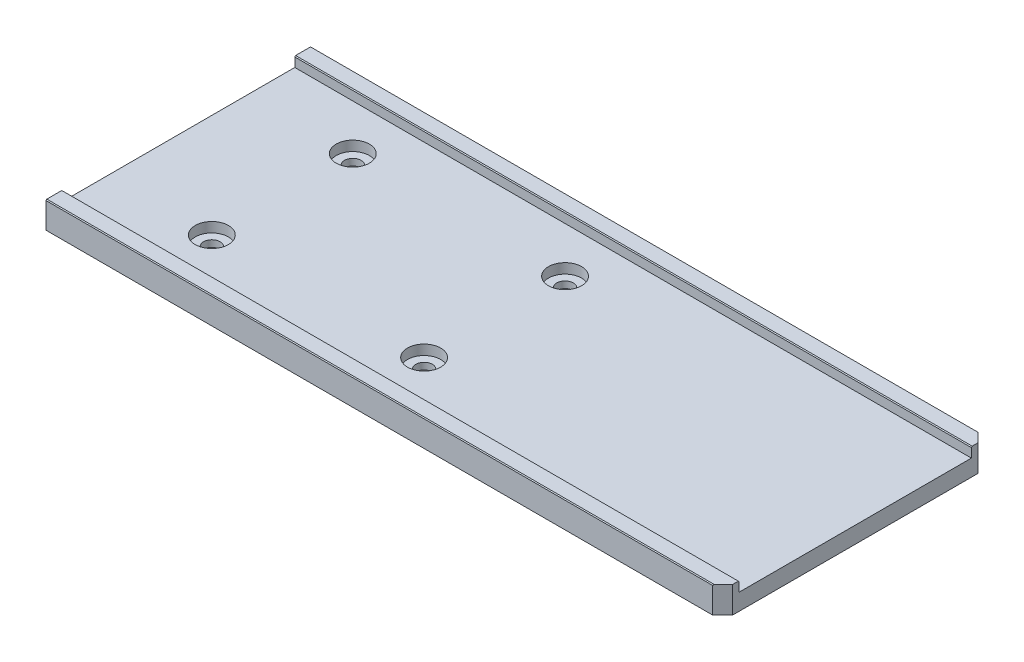
SolidWorks part; units mm, degrees
ref_plane "Front Plane" through (0, 0, 0) normal (0, 0, 1) x (1, 0, 0)
ref_plane "Top Plane" through (0, 0, 0) normal (0, 1, 0) x (1, 0, 0)
ref_plane "Right Plane" through (0, 0, 0) normal (1, 0, 0) x (0, 0, -1)
sketch "Sketch1" plane through (0, 0, 0) normal (0, 1, 0) x (1, 0, 0)
  line L1 (0, 0) -> (204, 0)
  line L2 (0, 0) -> (0, 80)
  line L3 (0, 80) -> (204, 80)
  line L4 (204, 0) -> (204, 80)
  dimension "D1" = 204
  dimension "D2" = 80
extrude "Boss-Extrude1" add sketch "Sketch1" along normal blind 8
sketch "Sketch2" plane through (0, 8, 0) normal (0, 1, 0) x (1, 0, 0)
  line L0 (0, 80) -> (0, 0) construction
  line L1 (0, 75) -> (204, 75)
  line L2 (0, 75) -> (0, 5)
  line L3 (0, 5) -> (204, 5)
  line L4 (204, 75) -> (204, 5)
  line L5 (204, 0) -> (204, 80) construction
  line L6 (204, 80) -> (0, 80) construction
  line L7 (0, 0) -> (204, 0) construction
  dimension "D1" = 5
  dimension "D2" = 5
extrude "Cut-Extrude1" cut sketch "Sketch2" against normal blind 3
sketch "Sketch3" plane through (0, 5, 0) normal (0, 1, 0) x (1, 0, 0)
  line L0 (204, 80) -> (0, 80) construction
  line L1 (0, 0) -> (204, 0) construction
  circle A0 centre (31.2471, 61.25) radius 5
  circle A1 centre (95.2471, 61.25) radius 5
  circle A2 centre (31.2471, 18.75) radius 5
  circle A3 centre (95.2471, 18.75) radius 5
  point P12 (0, 0)
  point P13 (0, 0)
  point P14 (0, 0)
  dimension "D3" = 10
  dimension "D1" = 18.75
  dimension "D2" = 18.75
  dimension "D4" = 64
extrude "Cut-Extrude2" cut sketch "Sketch3" against normal blind 3
sketch "Sketch4" plane through (0, 2, 0) normal (0, 1, 0) x (1, 0, 0)
  circle A0 centre (31.2471, 61.25) radius 2.5
  circle A1 centre (95.2471, 61.25) radius 2.5
  circle A2 centre (95.2471, 18.75) radius 2.5
  circle A3 centre (31.2471, 18.75) radius 2.5
  dimension "D1" = 5
extrude "Cut-Extrude3" cut sketch "Sketch4" against normal through all
chamfer "Chamfer1" distance 3 angle 45 2 edges at (204, 4, -80) (204, 4, 0)
chamfer "Chamfer2" distance 0.25 angle 45 4 edges at (102, 8, -75) (100.5, 8, -80) (102, 8, -5) (100.5, 8, 0)
